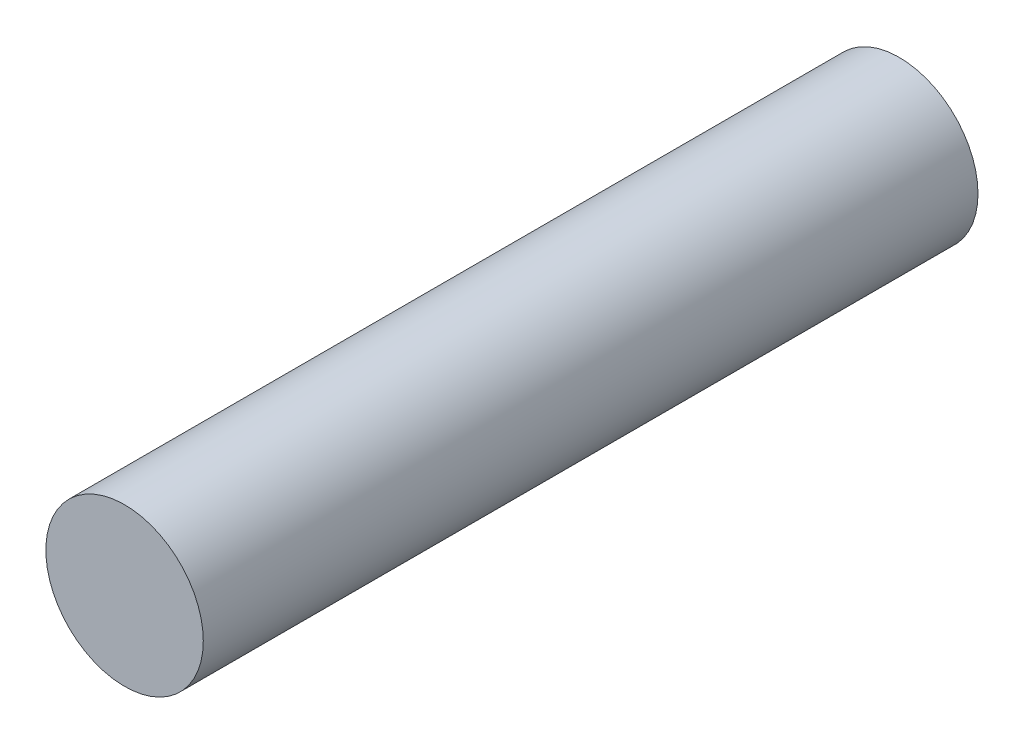
SolidWorks part; units mm, degrees
ref_plane "Front Plane" through (0, 0, 0) normal (0, 0, 1) x (1, 0, 0)
ref_plane "Top Plane" through (0, 0, 0) normal (0, 1, 0) x (1, 0, 0)
ref_plane "Right Plane" through (0, 0, 0) normal (1, 0, 0) x (0, 0, -1)
sketch "Sketch1" plane through (0, 0, 0) normal (0, 0, 1) x (1, 0, 0)
  circle A0 centre (0, 0) radius 8.001
  dimension "D1" = 16.002
extrude "Boss-Extrude1" add sketch "Sketch1" along normal blind 78.74
